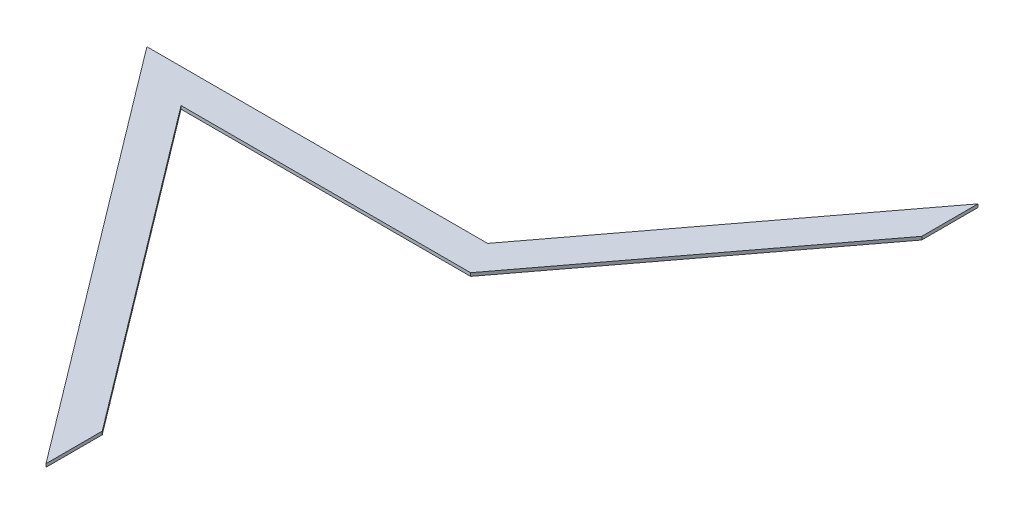
SolidWorks part; units mm, degrees
ref_plane "Front Plane" through (0, 0, 0) normal (0, 0, 1) x (1, 0, 0)
ref_plane "Top Plane" through (0, 0, 0) normal (0, 1, 0) x (1, 0, 0)
ref_plane "Right Plane" through (0, 0, 0) normal (1, 0, 0) x (0, 0, -1)
sketch "Sketch1" plane through (0, 0, 0) normal (0, 1, 0) x (1, 0, 0)
  line L1 (74.9994, 215) -> (75, 197.5)
  line L9 (0, 0) -> (0, 17.5)
  line L10 (0, 17.5) -> (-75.4822, 117.5)
  line L11 (-75.4822, 117.5) -> (14.6183, 117.5)
  line L12 (14.6183, 117.5) -> (75, 197.5)
  line L20 (74.9994, 215) -> (9.3645, 128.04)
  line L21 (9.3645, 128.04) -> (-96.6474, 128.04)
  line L22 (-96.6474, 128.04) -> (0, 0)
  point P0 (0, 0)
  dimension "D1" = 37.046
  dimension "D2" = 37.046
  dimension "D3" = 75
  dimension "D4" = 10.54
  dimension "D5" = 17.5
  dimension "D6" = 17.5
  dimension "D7" = 100
  dimension "D8" = 180
  dimension "D10" = 106.0119
extrude "Boss-Extrude1" add sketch "Sketch1" along normal blind 1
